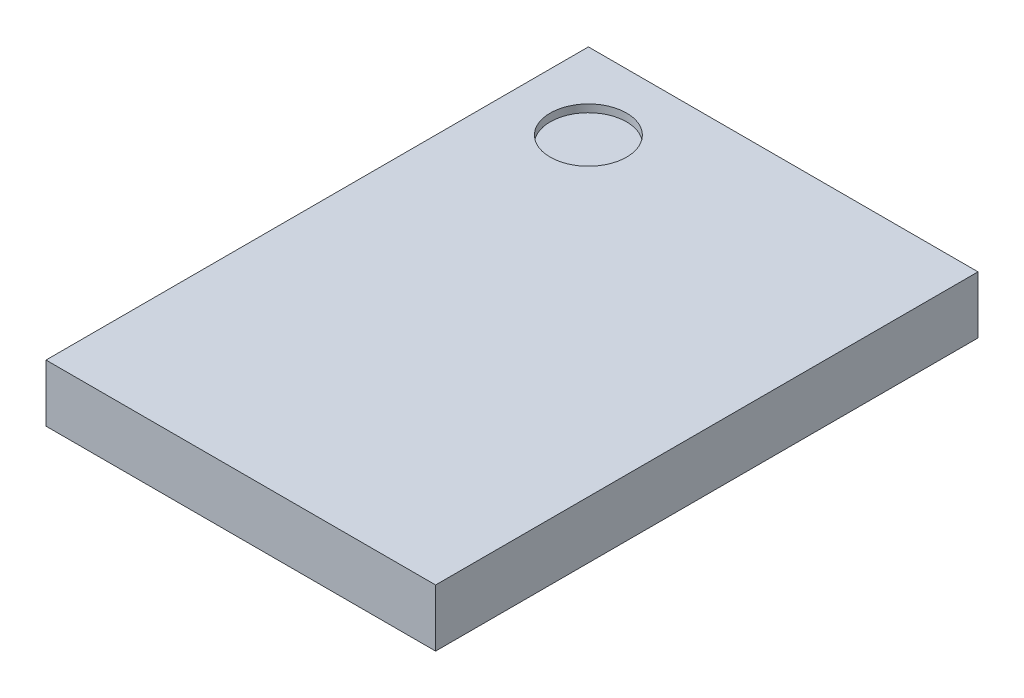
SolidWorks part; units mm, degrees
ref_plane "Front Plane" through (0, 0, 0) normal (0, 0, 1) x (1, 0, 0)
ref_plane "Top Plane" through (0, 0, 0) normal (0, 1, 0) x (1, 0, 0)
ref_plane "Right Plane" through (0, 0, 0) normal (1, 0, 0) x (0, 0, -1)
sketch "Sketch1" plane through (0, 0, 0) normal (0, 1, 0) x (1, 0, 0)
  line L1 (-2.55, -3.55) -> (2.55, -3.55)
  line L2 (-2.55, -3.55) -> (-2.55, 3.55)
  line L3 (-2.55, 3.55) -> (2.55, 3.55)
  line L4 (2.55, -3.55) -> (2.55, 3.55)
  line L5 (-2.55, -3.55) -> (2.55, 3.55) construction
  line L6 (-2.55, 3.55) -> (2.55, -3.55) construction
  point P0 (0, 0)
  dimension "D1" = 5.1
  dimension "D2" = 7.1
extrude "Boss-Extrude1" add sketch "Sketch1" along normal blind 0.75
sketch "Sketch2" plane through (0, 0.75, 0) normal (0, 1, 0) x (1, 0, 0)
  line L0 (-2.55, 3.55) -> (-2.55, -3.55) construction
  line L1 (2.55, 3.55) -> (-2.55, 3.55) construction
  circle A0 centre (-1.55, 2.55) radius 0.5
  dimension "D1" = 1
  dimension "D2" = 1
  dimension "D3" = 1
extrude "Cut-Extrude1" cut sketch "Sketch2" against normal blind 0.1
